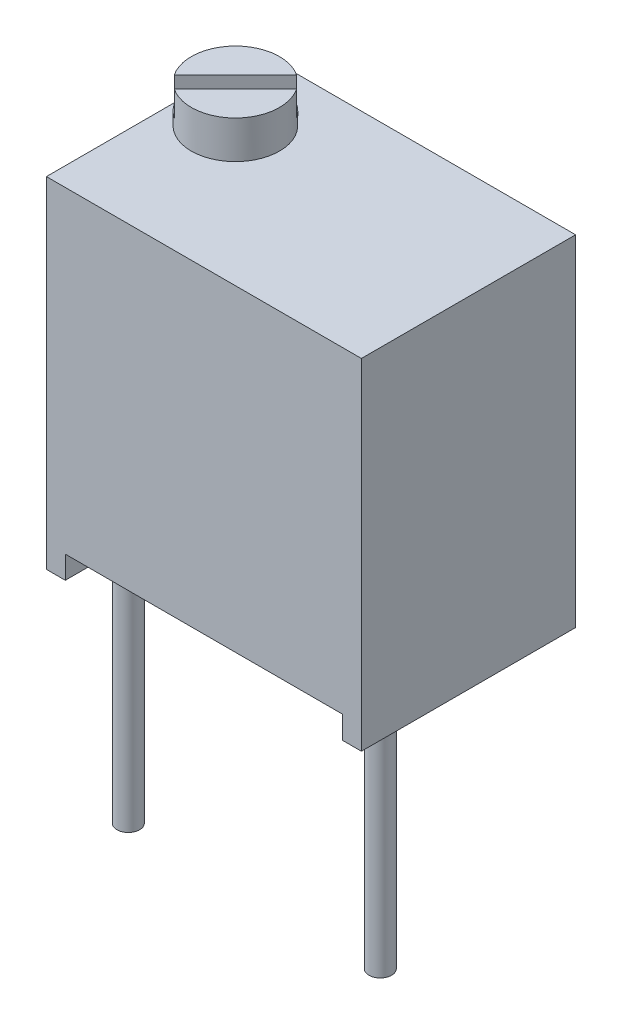
SolidWorks part; units mm, degrees
ref_plane "Front Plane" through (0, 0, 0) normal (0, 0, 1) x (1, 0, 0)
ref_plane "Top Plane" through (0, 0, 0) normal (0, 1, 0) x (1, 0, 0)
ref_plane "Right Plane" through (0, 0, 0) normal (1, 0, 0) x (0, 0, -1)
sketch "Sketch3" plane through (0, 0, 0) normal (0, 0, 1) x (1, 0, 0)
  line L1 (-0.635, 7.112) -> (5.715, 7.112)
  line L2 (-0.635, 7.112) -> (-0.635, 0.254)
  line L3 (-0.635, 0.254) -> (5.715, 0.254)
  line L4 (5.715, 7.112) -> (5.715, 0.254)
  dimension "D1" = 0.635
  dimension "D2" = 6.35
  dimension "D3" = 0.254
  dimension "D4" = 6.858
extrude "Base-Extrude" add sketch "Sketch3" against normal blind 3.302 and the other way blind 1.016
sketch "Sketch4" plane through (0, 0, 1.016) normal (0, 0, 1) x (1, 0, 0)
  line L0 (-0.635, 0.254) -> (5.715, 0.254) construction
  line L1 (-0.254, 0.7112) -> (5.334, 0.7112)
  line L2 (-0.254, 0.7112) -> (-0.254, 0.254)
  line L3 (-0.254, 0.254) -> (5.334, 0.254)
  line L4 (5.334, 0.7112) -> (5.334, 0.254)
  line L5 (5.715, 0.254) -> (5.715, 7.112) construction
  line L6 (-0.635, 7.112) -> (-0.635, 0.254) construction
  dimension "D1" = 0.4572
  dimension "D2" = 0.381
  dimension "D3" = 0.381
extrude "Cut-Extrude1" cut sketch "Sketch4" against normal through all
sketch "Sketch5" plane through (0, 7.112, 0) normal (0, 1, 0) x (-1, 0, 0)
  line L0 (-5.715, -3.302) -> (0.635, -3.302) construction
  line L1 (0.635, -3.302) -> (0.635, 1.016) construction
  circle A0 centre (-0.381, -1.778) radius 0.889
  dimension "D3" = 1.778
  dimension "D1" = 1.524
  dimension "D2" = 1.016
extrude "Boss-Extrude1" add sketch "Sketch5" along normal blind 0.762
sketch "Sketch6" plane through (0, 7.874, 0) normal (0, 1, 0) x (-1, 0, 0)
  line L0 (-1.1533, -2.8017) -> (0.6427, -1.0057)
  line L1 (-1.4047, -2.5503) -> (0.3913, -0.7543)
  line L2 (-1.1533, -2.8017) -> (-1.4047, -2.5503)
  line L3 (0.6427, -1.0057) -> (0.3913, -0.7543)
  line L4 (-0.381, -1.778) -> (-1.4942, -2.8912) construction
  line L5 (-0.381, -1.778) -> (-2.9469, -1.778) construction
  circle A0 centre (-0.381, -1.778) radius 0.889 construction
  dimension "D1" = 0.3556
  dimension "D2" = 0.1778
  dimension "D3" = 45
  dimension "D4" = 1.27
  dimension "D5" = 1.27
extrude "Cut-Extrude2" cut sketch "Sketch6" against normal blind 0.508
sketch "Sketch7" plane through (0, 0.7112, 0) normal (0, -1, 0) x (1, 0, 0)
  line L0 (0, 0) -> (5.4576, 0) construction
  circle A0 centre (0, 0) radius 0.2286
  circle A1 centre (5.08, 0) radius 0.2286
  circle A2 centre (2.54, -2.54) radius 0.2286
  dimension "D1" = 0.4572
  dimension "D2" = 5.08
  dimension "D3" = 2.54
  dimension "D4" = 2.54
extrude "Boss-Extrude2" add sketch "Sketch7" along normal blind 5.08
sketch "Component_Outline" plane through (0, 0, 0) normal (0, 1, 0) x (1, 0, 0)
  line L1 (-0.635, -1.016) -> (5.715, -1.016)
  line L2 (-0.635, -1.016) -> (-0.635, 3.302)
  line L3 (-0.635, 3.302) -> (5.715, 3.302)
  line L4 (5.715, -1.016) -> (5.715, 3.302)
